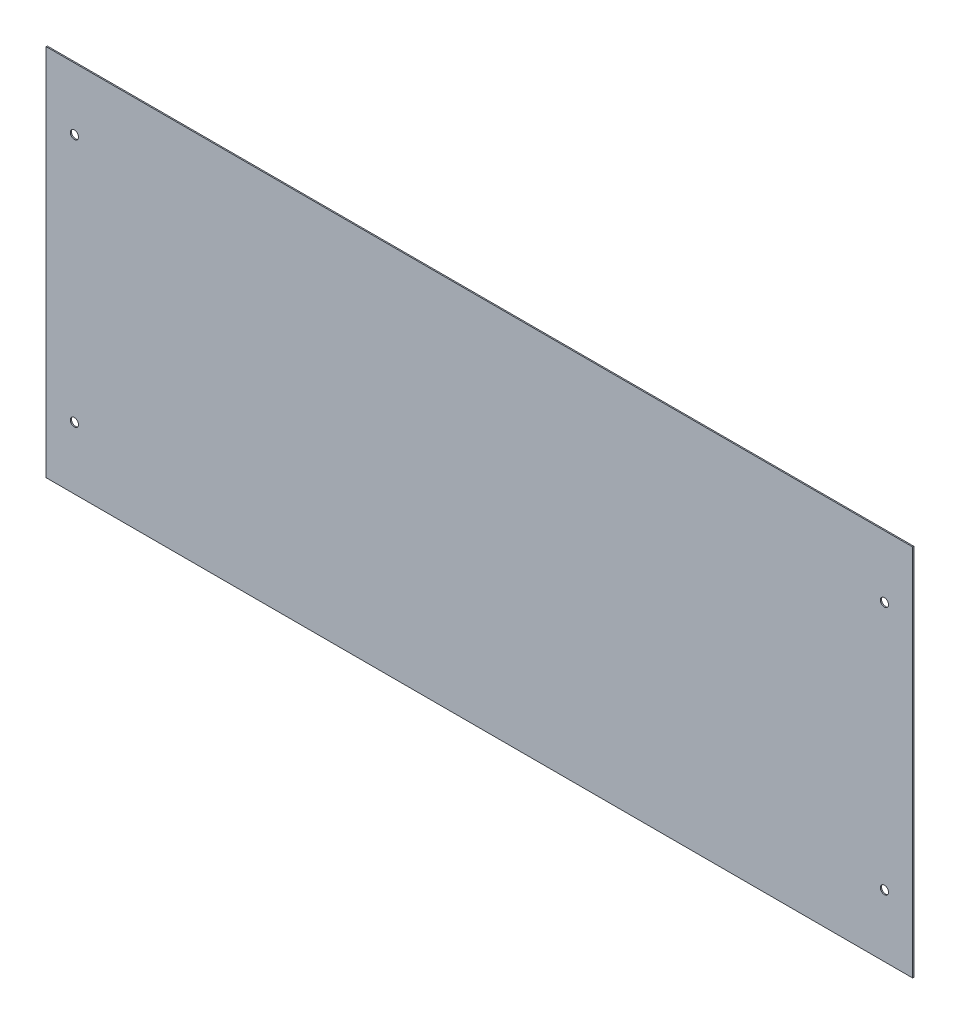
SolidWorks part; units mm, degrees
material "AISI 304"
ref_plane "Front Plane" through (0, 0, 0) normal (0, 0, 1) x (1, 0, 0)
ref_plane "Top Plane" through (0, 0, 0) normal (0, 1, 0) x (1, 0, 0)
ref_plane "Right Plane" through (0, 0, 0) normal (1, 0, 0) x (0, 0, -1)
sketch "Sketch1" plane through (0, 0, 0) normal (0, 0, 1) x (1, 0, 0)
  line L1 (0, 0) -> (738, 0)
  line L2 (0, 0) -> (0, 318)
  line L3 (0, 318) -> (738, 318)
  line L4 (738, 0) -> (738, 318)
  circle A8 centre (24, 265.06) radius 3.5
  circle A9 centre (714, 265.06) radius 3.5
  circle A10 centre (714, 52.94) radius 3.5
  circle A11 centre (24, 52.94) radius 3.5
  dimension "D3" = 7
  dimension "D7" = 52.94
  dimension "D1" = 318
  dimension "D2" = 738
  dimension "D4" = 24
  dimension "D5" = 24
  dimension "D6" = 52.94
extrude "Boss-Extrude1" add sketch "Sketch1" along normal blind 1
